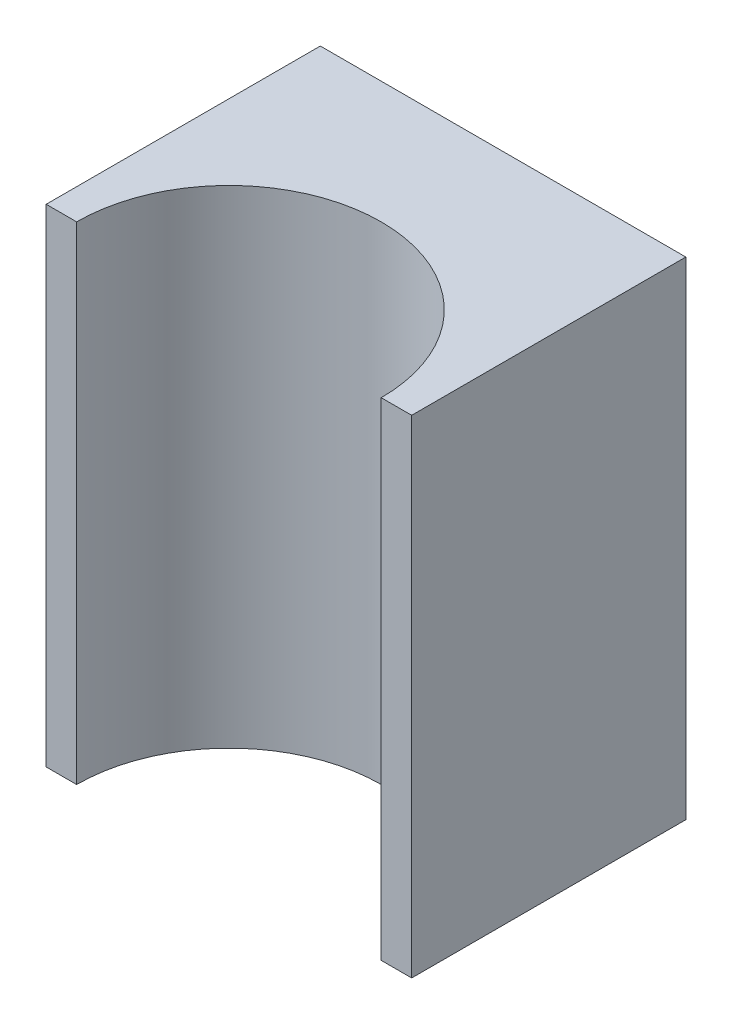
SolidWorks part; units mm, degrees
ref_plane "Plan de face" through (0, 0, 0) normal (0, 0, 1) x (1, 0, 0)
ref_plane "Plan de dessus" through (0, 0, 0) normal (0, 1, 0) x (1, 0, 0)
ref_plane "Plan de droite" through (0, 0, 0) normal (1, 0, 0) x (0, 0, -1)
sketch "Esquisse1" plane through (0, 0, 0) normal (0, 1, 0) x (1, 0, 0)
  line L0 (0.25, -0.225) -> (0.3, -0.225)
  line L1 (-0.3, 0.225) -> (0.3, 0.225)
  line L2 (-0.3, 0.225) -> (-0.3, -0.225)
  line L3 (-0.3, -0.225) -> (-0.25, -0.225)
  line L4 (0.3, 0.225) -> (0.3, -0.225)
  line L5 (-0.3, 0.225) -> (0.3, -0.225) construction
  line L6 (-0.3, -0.225) -> (0.3, 0.225) construction
  arc A0 (0.25, -0.225) -> (-0.25, -0.225) centre (0, -0.225) ccw
  point P0 (0, 0)
  dimension "D3" = 0.5
  dimension "D1" = 0.6
  dimension "D2" = 0.45
extrude "Boss.-Extru.1" add sketch "Esquisse1" along normal blind 0.8
